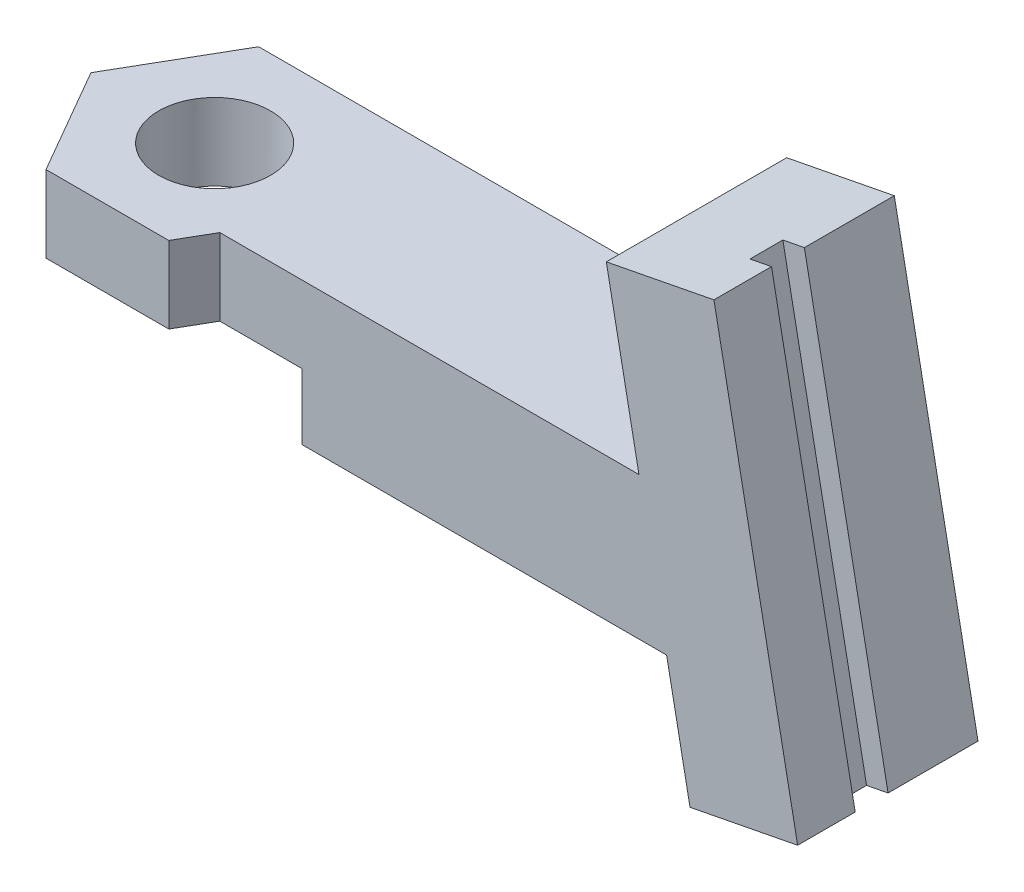
SolidWorks part; units mm, degrees
ref_plane "Front Plane" through (0, 0, 0) normal (0, 0, 1) x (1, 0, 0)
ref_plane "Top Plane" through (0, 0, 0) normal (0, 1, 0) x (1, 0, 0)
ref_plane "Right Plane" through (0, 0, 0) normal (1, 0, 0) x (0, 0, -1)
sketch "Sketch1" plane through (0, 0, 0) normal (0, 1, 0) x (1, 0, 0)
  line L1 (0, 0) -> (25, 0)
  line L2 (0, 0) -> (0, -6.75)
  line L3 (0, -6.75) -> (25, -6.75)
  line L4 (25, 0) -> (25, -6.75)
  dimension "D1" = 6.75
  dimension "D2" = 25
extrude "Boss-Extrude1" add sketch "Sketch1" along normal blind 6.5
ref_plane "Plane1" through (0, 0, 3.375) normal (0, 0, 1) x (1, 0, 0)
sketch "Sketch3" plane through (0, 0, 3.375) normal (0, 0, 1) x (1, 0, 0)
  line L0 (21.2757, 14.1555) -> (26.1838, 15.1096)
  line L1 (26.1838, 15.1096) -> (30, -4.523)
  line L2 (30, -4.523) -> (25.0919, -5.477)
  line L3 (25.0919, -5.477) -> (21.2757, 14.1555)
  line L4 (0, 6.5) -> (25, 6.5) construction
  line L5 (0, 6.5) -> (0, 0) construction
  point P6 (27.5459, -5)
  dimension "D1" = 30
  dimension "D2" = 5
  dimension "D3" = 20
  dimension "D4" = 79
  dimension "D6" = 5
extrude "Boss-Extrude3" add sketch "Sketch3" against normal up to surface and the other way up to surface up to face at (12.5, 3.25, 0) other way up to face at (12.5, 3.25, 6.75)
sketch "Sketch4" plane through (-1.8768, 9.6551, 0) normal (-0.1908, 0.9816, 0) x (0.9816, 0.1908, 0)
  line L0 (28.5858, -6.75) -> (28.5858, 0) construction
  line L1 (27.5858, -2.625) -> (28.5858, -2.625)
  line L2 (27.5858, -2.625) -> (27.5858, -4.125)
  line L3 (27.5858, -4.125) -> (28.5858, -4.125)
  line L4 (28.5858, -2.625) -> (28.5858, -4.125)
  point P6 (28.5858, -3.375)
  dimension "D1" = 1.5
  dimension "D2" = 1
extrude "Cut-Extrude1" cut sketch "Sketch4" against normal blind 23 contours L2 L3 L4 L1
sketch "Sketch5" plane through (0, 6.5, 0) normal (0, 1, 0) x (1, 0, 0)
  line L0 (0, 0) -> (0, -6.75) construction
  line L1 (-5.6003, -3.375) -> (-2.8001, -8.225)
  line L2 (-2.8001, -8.225) -> (2.8001, -8.225)
  line L3 (2.8001, -8.225) -> (5.6003, -3.375)
  line L4 (5.6003, -3.375) -> (2.8001, 1.475)
  line L5 (2.8001, 1.475) -> (-2.8001, 1.475)
  line L6 (-2.8001, 1.475) -> (-5.6003, -3.375)
  circle A0 centre (0, -3.375) radius 4.85 construction
  dimension "D1" = 4.85
extrude "Boss-Extrude4" add sketch "Sketch5" against normal up to surface (6.5 mm away) up to face at (12.0136, 0, 3.375)
sketch "Sketch6" plane through (0, 6.5, 0) normal (0, 1, 0) x (1, 0, 0)
  circle A0 centre (0, -3.3356) radius 2.55
  dimension "D1" = 5.1
extrude "Cut-Extrude2" cut sketch "Sketch6" against normal blind 10
sketch "Sketch7" plane through (0, 0, -1.475) normal (0, 0, -1) x (-1, 0, 0)
  line L0 (-2.8001, 0) -> (-24.0272, 0)
  line L1 (-24.0272, 0) -> (-25.0919, -5.477)
  line L2 (-25.0919, -5.477) -> (-30, -4.523)
  line L3 (-30, -4.523) -> (-26.1838, 15.1096)
  line L4 (-26.1838, 15.1096) -> (-21.2757, 14.1555)
  line L5 (-21.2757, 14.1555) -> (-22.7638, 6.5)
  line L6 (-22.7638, 6.5) -> (-2.8001, 6.5)
  line L7 (-2.8001, 6.5) -> (-2.8001, 0)
extrude "Boss-Extrude5" add sketch "Sketch7" against normal up to surface (1.475 mm away) up to face at (19.5807, 4.0331, 0)
sketch "Sketch8" plane through (0, 0, 0) normal (0, -1, 0) x (-1, 0, 0)
  line L1 (-4.6765, -11.475) -> (4.6765, -11.475)
  line L2 (4.6765, -11.475) -> (9.3531, -3.375)
  line L3 (9.3531, -3.375) -> (4.6765, 4.725)
  line L4 (4.6765, 4.725) -> (-4.6765, 4.725)
  line L5 (-4.6765, 4.725) -> (-9.3531, -3.375)
  line L6 (-9.3531, -3.375) -> (-4.6765, -11.475)
  circle A0 centre (0, -3.375) radius 8.1 construction
  dimension "D1" = 16.2
extrude "Cut-Extrude3" cut sketch "Sketch8" against normal blind 3
